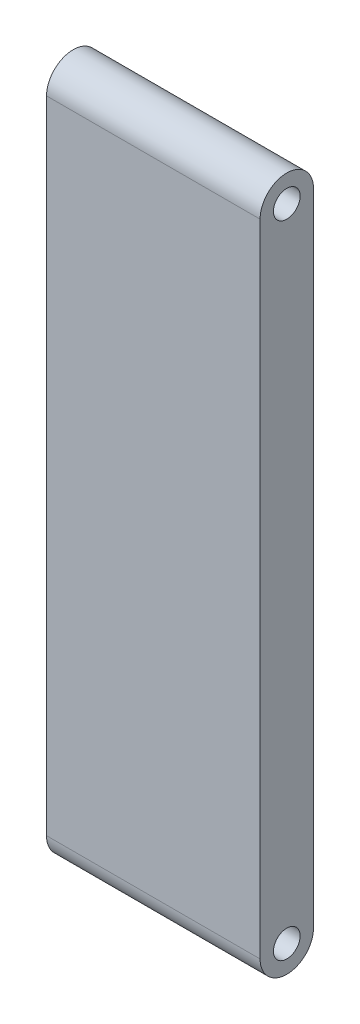
SolidWorks part; units mm, degrees
ref_plane "Front" through (0, 0, 0) normal (0, 0, 1) x (1, 0, 0)
ref_plane "Top" through (0, 0, 0) normal (0, 1, 0) x (1, 0, 0)
ref_plane "Right" through (0, 0, 0) normal (1, 0, 0) x (0, 0, -1)
sketch "Sketch1" plane through (0, 0, 0) normal (0, 0, 1) x (1, 0, 0)
  line L1 (0, 0) -> (20, 0)
  line L2 (0, 0) -> (0, 60)
  line L3 (0, 60) -> (20, 60)
  line L4 (20, 0) -> (20, 60)
  dimension "D1" = 60
  dimension "D2" = 20
extrude "Boss-Extrude1" add sketch "Sketch1" along normal blind 5
sketch "Sketch2" plane through (20, 0, 0) normal (1, 0, 0) x (0, 0, -1)
  line L0 (-5, 60) -> (0, 60) construction
  circle A0 centre (-2.5, 60) radius 2.5
  circle A1 centre (-2.5, 60) radius 1.25
  dimension "D1" = 2.5
extrude "Boss-Extrude2" add sketch "Sketch2" against normal up to surface (20 mm away) up to face at (0, 30, 2.5)
sketch "Sketch3" plane through (0, 0, 0) normal (-1, 0, 0) x (0, 0, 1)
  line L0 (3.75, 60) -> (1.25, 60) construction
  circle A0 centre (2.5, 60) radius 1.25
extrude "Cut-Extrude1" cut sketch "Sketch3" against normal blind 29
sketch "Sketch4" plane through (0, 0, 0) normal (-1, 0, 0) x (0, 0, 1)
  line L0 (5, 0) -> (0, 0) construction
  circle A0 centre (2.5, 0) radius 2.5
  circle A1 centre (2.5, 0) radius 1.25
  dimension "D1" = 2.5
extrude "Boss-Extrude3" add sketch "Sketch4" against normal up to surface (20 mm away) up to face at (20, 30.625, 2.5)
sketch "Sketch5" plane through (20, 0, 0) normal (1, 0, 0) x (0, 0, -1)
  line L0 (-3.75, 0) -> (-1.25, 0) construction
  circle A0 centre (-2.5, 0) radius 1.25
extrude "Cut-Extrude2" cut sketch "Sketch5" against normal blind 29
